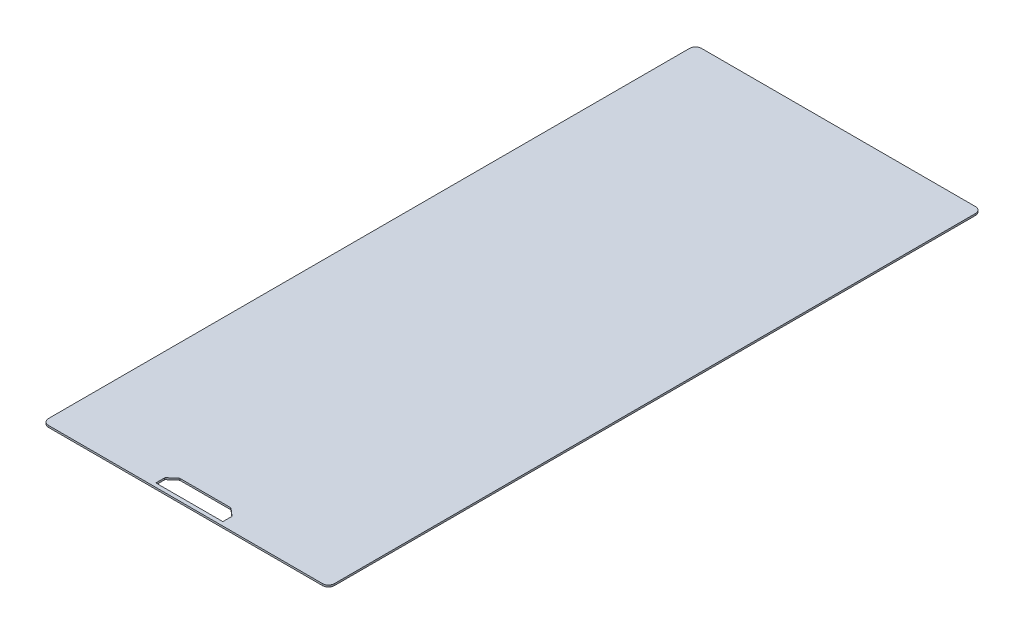
SolidWorks part; units mm, degrees
ref_plane "Front Plane" through (0, 0, 0) normal (0, 0, 1) x (1, 0, 0)
ref_plane "Top Plane" through (0, 0, 0) normal (0, 1, 0) x (1, 0, 0)
ref_plane "Right Plane" through (0, 0, 0) normal (1, 0, 0) x (0, 0, -1)
sketch "Sketch1" plane through (0, 0, 0) normal (0, 1, 0) x (1, 0, 0)
  line L1 (-231.5, -551.5) -> (231.5, -551.5)
  line L2 (-241.5, -541.5) -> (-241.5, 541.5)
  line L3 (-231.5, 551.5) -> (231.5, 551.5)
  line L4 (241.5, -541.5) -> (241.5, 541.5)
  line L5 (-241.5, -551.5) -> (241.5, 551.5) construction
  line L6 (-241.5, 551.5) -> (241.5, -551.5) construction
  arc A0 (231.5, -551.5) -> (241.5, -541.5) centre (231.5, -541.5) ccw
  arc A1 (-231.5, -551.5) -> (-241.5, -541.5) centre (-231.5, -541.5) cw
  arc A2 (-241.5, 541.5) -> (-231.5, 551.5) centre (-231.5, 541.5) cw
  arc A3 (231.5, 551.5) -> (241.5, 541.5) centre (231.5, 541.5) cw
  point P0 (0, 0)
  dimension "D3" = 10
  dimension "D1" = 483
  dimension "D2" = 1103
extrude "Boss-Extrude1" add sketch "Sketch1" along normal blind 3
sketch "Sketch2" plane through (0, 3, 0) normal (0, 1, 0) x (1, 0, 0)
  line L0 (0, -551.5) -> (0, -545) construction
  line L1 (-231.5, -551.5) -> (231.5, -551.5) construction
  line L2 (-56.625, -545) -> (56.625, -545)
  line L3 (56.625, -545) -> (56.625, -530.6446)
  line L4 (55.7585, -528.7521) -> (44.0052, -518.6075)
  line L5 (42.3717, -518) -> (-42.3717, -518)
  line L6 (-44.0052, -518.6075) -> (-55.7585, -528.7521)
  line L7 (-56.625, -530.6446) -> (-56.625, -545)
  arc A0 (56.625, -530.6446) -> (55.7585, -528.7521) centre (54.125, -530.6446) ccw
  arc A1 (44.0052, -518.6075) -> (42.3717, -518) centre (42.3717, -520.5) ccw
  arc A2 (-55.7585, -528.7521) -> (-56.625, -530.6446) centre (-54.125, -530.6446) ccw
  arc A3 (-42.3717, -518) -> (-44.0052, -518.6075) centre (-42.3717, -520.5) ccw
  point P8 (0, -545)
  point P15 (56.625, -529.5)
  point P18 (43.3014, -518)
  point P23 (-43.3014, -518)
  dimension "D6" = 2.5
  dimension "D1" = 113.25
  dimension "D2" = 15.5
  dimension "D3" = 27
  dimension "D4" = 86.6028
  dimension "D5" = 6.5
extrude "Cut-Extrude1" cut sketch "Sketch2" against normal through all
